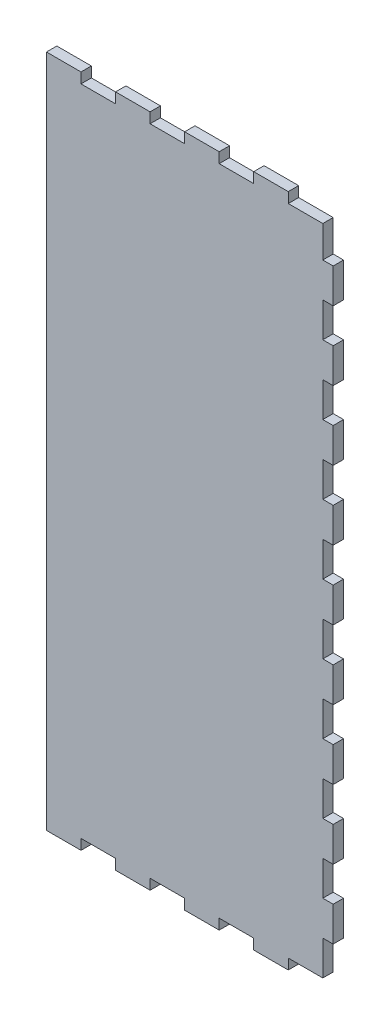
SolidWorks part; units mm, degrees
ref_plane "Plan de face" through (0, 0, 0) normal (0, 0, 1) x (1, 0, 0)
ref_plane "Plan de dessus" through (0, 0, 0) normal (0, 1, 0) x (1, 0, 0)
ref_plane "Plan de droite" through (0, 0, 0) normal (1, 0, 0) x (0, 0, -1)
sketch "Esquisse1" plane through (0, 0, 0) normal (0, 0, 1) x (1, 0, 0)
  line L1 (0, 0) -> (80, 0)
  line L2 (0, 0) -> (0, -189.15)
  line L3 (0, -189.15) -> (80, -189.15)
  line L4 (80, 0) -> (80, -189.15)
  dimension "D1" = 80
  dimension "D2" = 189.15
extrude "Boss.-Extru.1" add sketch "Esquisse1" along normal blind 3
sketch "Esquisse3" plane through (0, 0, 0) normal (0, 1, 0) x (1, 0, 0)
  line L0 (80, -3) -> (0, -3) construction
  line L1 (0, 0) -> (10, 0)
  line L2 (0, 0) -> (0, -3)
  line L3 (0, -3) -> (10, -3)
  line L4 (10, 0) -> (10, -3)
  dimension "D1" = 10
extrude "Boss.-Extru.2" add sketch "Esquisse3" along normal blind 3
pattern_linear "Répétition linéaire1" count 4 spacing 20 along (1, 0, 0) of "Boss.-Extru.2"
sketch "Esquisse4" plane through (0, -189.15, 0) normal (0, -1, 0) x (1, 0, 0)
  line L0 (0, 0) -> (80, 0) construction
  line L1 (0, 3) -> (10, 3)
  line L2 (0, 3) -> (0, 0)
  line L3 (0, 0) -> (10, 0)
  line L4 (10, 3) -> (10, 0)
  dimension "D1" = 10
extrude "Boss.-Extru.3" add sketch "Esquisse4" along normal blind 3
pattern_linear "Répétition linéaire2" count 4 spacing 20 along (1, 0, 0) of "Boss.-Extru.3"
sketch "Esquisse5" plane through (80, 0, 0) normal (1, 0, 0) x (0, 0, -1)
  line L0 (-3, -189.15) -> (-3, 0) construction
  line L1 (-3, -179.15) -> (0, -179.15)
  line L2 (-3, -179.15) -> (-3, -169.15)
  line L3 (-3, -169.15) -> (0, -169.15)
  line L4 (0, -179.15) -> (0, -169.15)
  line L5 (0, -189.15) -> (0, 0) construction
  line L6 (-3, -189.15) -> (0, -189.15) construction
  dimension "D1" = 10
  dimension "D2" = 10
extrude "Boss.-Extru.4" add sketch "Esquisse5" along normal blind 3
pattern_linear "Répétition linéaire3" count 9 spacing 20 along (0, 1, 0) of "Boss.-Extru.4"
